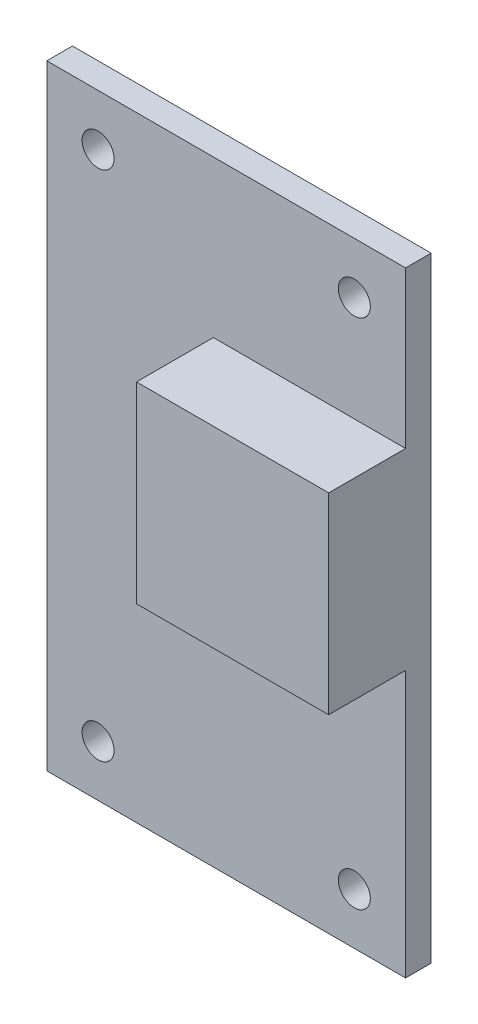
SolidWorks part; units mm, degrees
ref_plane "Alzado" through (0, 0, 0) normal (0, 0, 1) x (1, 0, 0)
ref_plane "Planta" through (0, 0, 0) normal (0, 1, 0) x (1, 0, 0)
ref_plane "Vista lateral" through (0, 0, 0) normal (1, 0, 0) x (0, 0, -1)
sketch "Croquis1" plane through (0, 0, 0) normal (0, 0, 1) x (1, 0, 0)
  line L1 (-14, -24) -> (14, -24)
  line L2 (-14, -24) -> (-14, 24)
  line L3 (-14, 24) -> (14, 24)
  line L4 (14, -24) -> (14, 24)
  line L5 (-14, -24) -> (14, 24) construction
  line L6 (-14, 24) -> (14, -24) construction
  point P0 (0, 0)
extrude "Saliente-Extruir1" add sketch "Croquis1" along normal blind 2
sketch "Croquis2" plane through (0, 0, 2) normal (0, 0, 1) x (1, 0, 0)
  line L0 (-14, 24) -> (-14, 20) construction
  line L1 (-14, 24) -> (-14, -24) construction
  line L2 (-14, 20) -> (-10, 20) construction
  line L3 (14, 24) -> (14, 20) construction
  line L4 (14, -24) -> (14, 24) construction
  line L5 (14, 20) -> (10, 20) construction
  line L6 (-14, -24) -> (-14, -20) construction
  line L7 (-14, -20) -> (-10, -20) construction
  line L8 (14, -24) -> (14, -20) construction
  line L9 (14, -20) -> (10, -20) construction
  circle A0 centre (-10, 20) radius 1.25
  circle A1 centre (10, 20) radius 1.25
  circle A2 centre (10, -20) radius 1.25
  circle A3 centre (-10, -20) radius 1.25
extrude "Cortar-Extruir1" cut sketch "Croquis2" against normal through all
sketch "Croquis3" plane through (0, 0, 2) normal (0, 0, 1) x (1, 0, 0)
  line L0 (14, -24) -> (14, 24) construction
  line L1 (14, 11.7931) -> (-1, 11.7931)
  line L2 (14, 11.7931) -> (14, -3.2069)
  line L3 (14, -3.2069) -> (-1, -3.2069)
  line L4 (-1, 11.7931) -> (-1, -3.2069)
extrude "Saliente-Extruir2" add sketch "Croquis3" along normal blind 6
